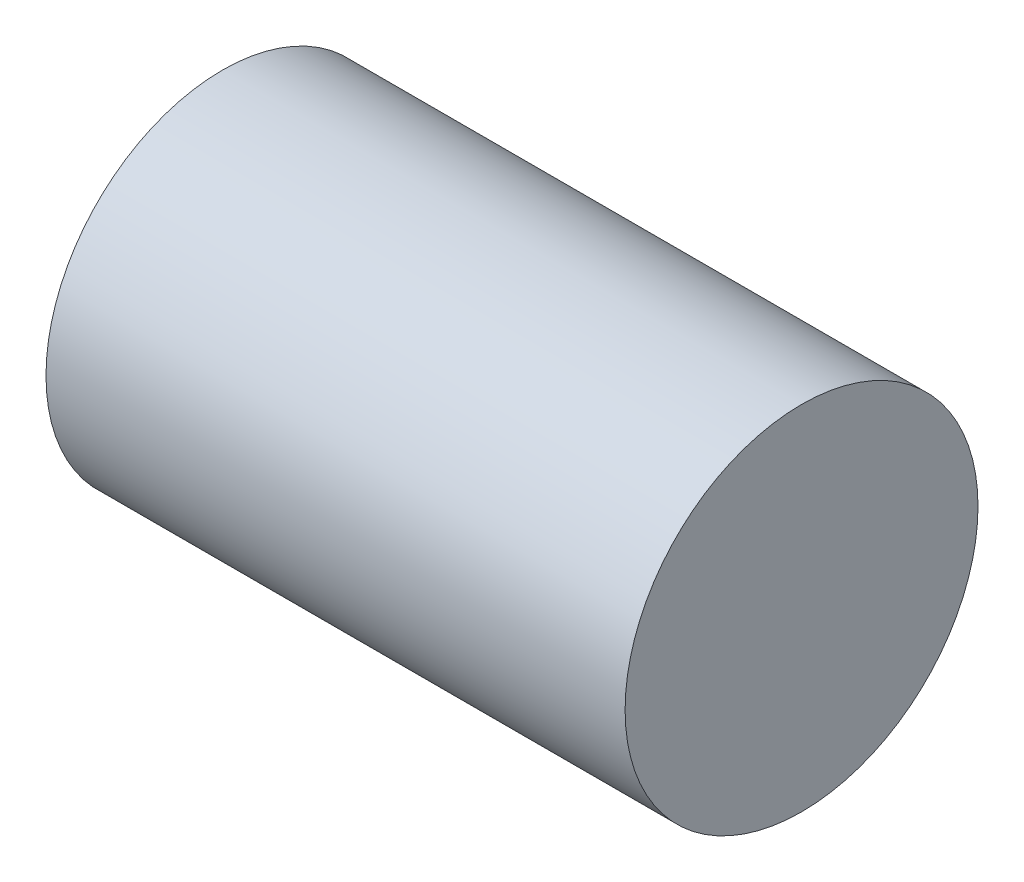
SolidWorks part; units mm, degrees
ref_plane "Front Plane" through (0, 0, 0) normal (0, 0, 1) x (1, 0, 0)
ref_plane "Top Plane" through (0, 0, 0) normal (0, 1, 0) x (1, 0, 0)
ref_plane "Right Plane" through (0, 0, 0) normal (1, 0, 0) x (0, 0, -1)
sketch "Sketch2" plane through (0, 0, 0) normal (1, 0, 0) x (0, 0, -1)
  circle A0 centre (0, 0) radius 19.5
  dimension "D1" = 39
extrude "Boss-Extrude1" add sketch "Sketch2" along normal blind 64
sketch "Sketch3" plane through (0, 0, 0) normal (-1, 0, 0) x (0, 0, 1)
  circle A0 centre (0, 0) radius 8
  dimension "D1" = 16
extrude "Cut-Extrude1" cut sketch "Sketch3" against normal blind 50
